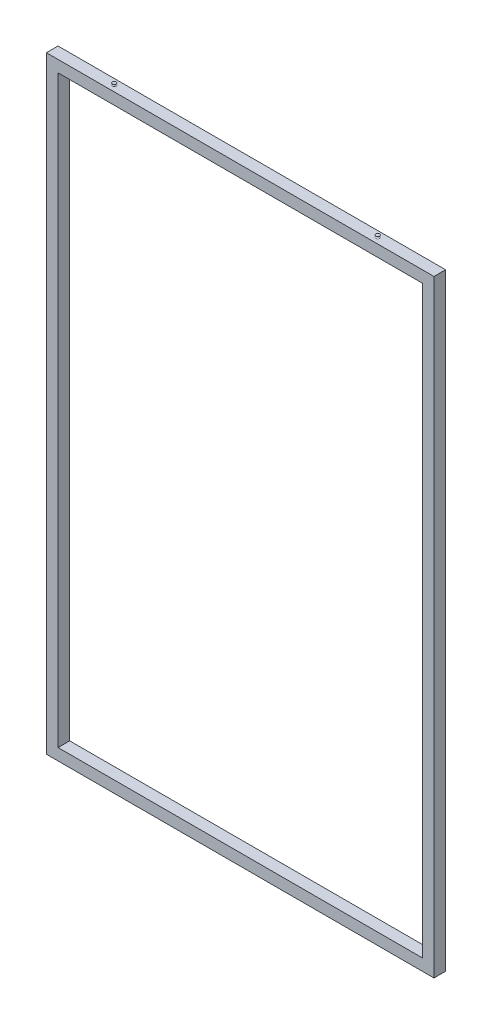
SolidWorks part; units mm, degrees
ref_plane "Front Plane" through (0, 0, 0) normal (0, 0, 1) x (1, 0, 0)
ref_plane "Top Plane" through (0, 0, 0) normal (0, 1, 0) x (1, 0, 0)
ref_plane "Right Plane" through (0, 0, 0) normal (1, 0, 0) x (0, 0, -1)
sketch "Sketch1" plane through (0, 0, 0) normal (0, 0, 1) x (1, 0, 0)
  line L0 (-470, 753.875) -> (470, 753.875)
  line L1 (-500, 783.875) -> (500, 783.875)
  line L2 (-500, 783.875) -> (-500, -783.875)
  line L3 (-500, -783.875) -> (500, -783.875)
  line L4 (500, 783.875) -> (500, -783.875)
  line L5 (-500, 783.875) -> (500, -783.875) construction
  line L6 (-500, -783.875) -> (500, 783.875) construction
  line L7 (470, 753.875) -> (470, -753.875)
  line L8 (-470, -753.875) -> (470, -753.875)
  line L9 (-470, 753.875) -> (-470, -753.875)
  point P0 (0, 0)
  dimension "D1" = 1567.75
  dimension "D2" = 1000
  dimension "D3" = 30
extrude "Boss-Extrude1" add sketch "Sketch1" along normal mid plane 30
sketch "Sketch2" plane through (0, 0, 0) normal (1, 0, 0) x (0, 0, -1)
  line L3 (-15, 783.875) -> (15, 783.875) construction
  line L4 (-15, 753.875) -> (15, 753.875) construction
  line L5 (-15, 783.875) -> (15, 783.875) construction
  line L6 (-15, 753.875) -> (15, 753.875) construction
  line L7 (-15, 783.875) -> (-15, 753.875) construction
  line L8 (15, 783.875) -> (15, 753.875) construction
  line L10 (13, 781.875) -> (13, 755.875)
  line L11 (-13, 755.875) -> (13, 755.875)
  line L12 (-13, 781.875) -> (-13, 755.875)
  line L13 (-13, 781.875) -> (13, 781.875)
  dimension "D1" = 2
sketch "Sketch4" plane through (0, 0, 0) normal (0, 0, 1) x (1, 0, 0)
  line L0 (-485, 768.875) -> (-485, -768.875)
  line L1 (-485, -768.875) -> (485, -768.875)
  line L2 (485, -768.875) -> (485, 768.875)
  line L3 (485, 768.875) -> (-485, 768.875)
  line L4 (500, -783.875) -> (500, 783.875)
  line L5 (500, 783.875) -> (-500, 783.875)
  line L6 (-500, 783.875) -> (-500, -783.875)
  line L7 (-500, -783.875) -> (500, -783.875)
  line L8 (500, -783.875) -> (500, 783.875)
  line L9 (500, 783.875) -> (-500, 783.875)
  line L10 (-500, 783.875) -> (-500, -783.875)
  line L11 (-500, -783.875) -> (500, -783.875)
  dimension "D1" = 0
  dimension "D2" = 15
sweep "Cut-Sweep1" cut profiles "Sketch2" path "Sketch4"
sketch "Sketch5" plane through (0, 783.875, 0) normal (0, 1, 0) x (1, 0, 0)
  line L0 (0, 18.3123) -> (0, -18.3123) construction
  line L6 (500, 15) -> (-500, 15)
  line L7 (-500, 15) -> (-500, -15)
  line L8 (-500, -15) -> (500, -15)
  line L9 (500, -15) -> (500, 15)
  line L10 (500, 15) -> (-500, 15)
  line L11 (-500, 15) -> (-500, -15)
  line L12 (-500, -15) -> (500, -15)
  line L13 (500, -15) -> (500, 15)
  circle A0 centre (-340, 0) radius 15 construction
  circle A1 centre (-340, 0) radius 7
  point P4 (0, 0)
  dimension "D1" = 340
  dimension "D2" = 0
  dimension "D3" = 8
ref_plane "Plane1" through (0, 790.675, 0) normal (0, 1, 0) x (1, 0, 0)
sketch "Sketch6" plane through (0, 790.675, 0) normal (0, 1, 0) x (1, 0, 0)
  circle A2 centre (-340, 0) radius 7 construction
  circle A3 centre (-340, 0) radius 7
sketch "Sketch7" plane through (0, 0, 0) normal (0, 0, 1) x (1, 0, 0)
  line L5 (-340, 783.875) -> (-340, 788.875)
  line L6 (-345, 788.875) -> (-340, 788.875)
  line L7 (-345, 783.875) -> (-340, 783.875)
  line L8 (-340, 795.1043) -> (-340, 811.1427) construction
  arc A0 (-345, 783.875) -> (-345, 788.875) centre (-345, 786.375) ccw
  point P12 (-340, 786.375)
  dimension "D1" = 2.5
  dimension "D2" = 5
revolve "Revolve1" add sketch "Sketch7" angle 360 about L8
mirror "Mirror1" about plane through (0, 0, 0) normal (1, 0, 0) of "Revolve1"
sketch "Sketch8" plane through (0, 788.875, 0) normal (0, 1, 0) x (1, 0, 0)
  circle A1 centre (340, 0) radius 5
  circle A2 centre (340, 0) radius 5
  point P0 (335, 0)
  dimension "D1" = 0
sketch "Sketch9" plane through (0, 0, 15) normal (0, 0, 1) x (1, 0, 0)
  line L0 (345, 788.875) -> (335, 788.875) construction
  line L1 (345, 788.875) -> (335, 788.875)
  point P2 (340, 788.875)
ref_plane "Plane2" through (340, 788.875, 15) normal (1, 0, 0) x (0, 0, -1)
ref_plane "Plane3" through (500, -783.875, 15) normal (0, 0, -1) x (-1, 0, 0)
